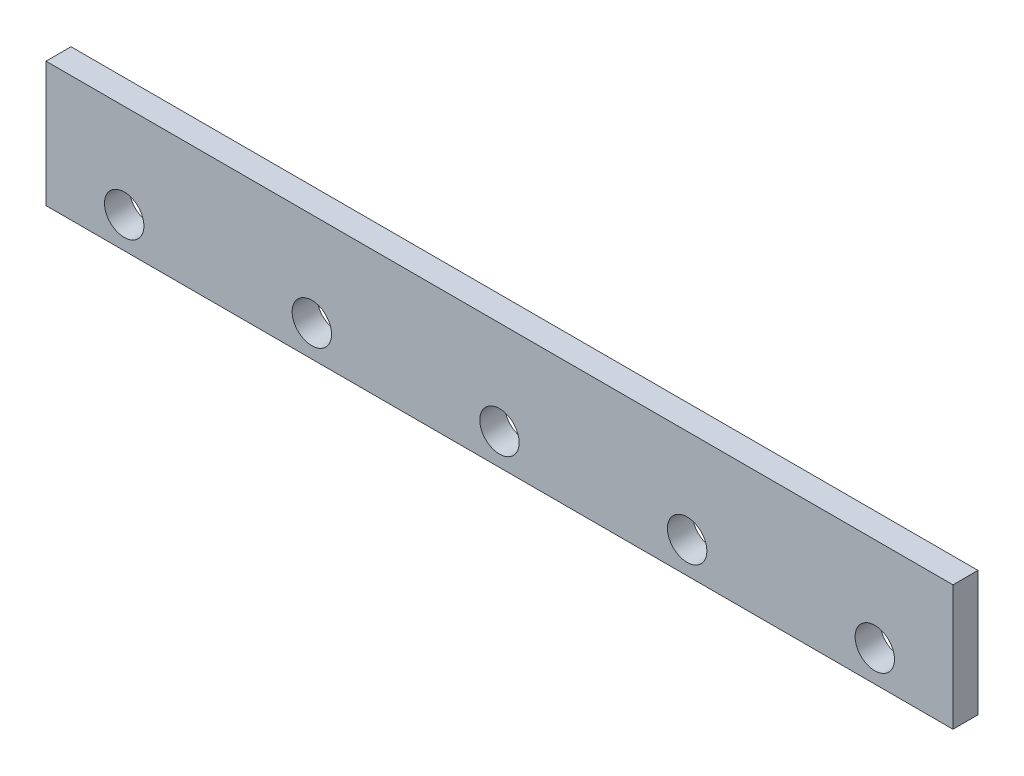
SolidWorks part; units mm, degrees
ref_plane "Front Plane" through (0, 0, 0) normal (0, 0, 1) x (1, 0, 0)
ref_plane "Top Plane" through (0, 0, 0) normal (0, 1, 0) x (1, 0, 0)
ref_plane "Right Plane" through (0, 0, 0) normal (1, 0, 0) x (0, 0, -1)
sketch "Sketch1" plane through (0, 0, 0) normal (0, 0, 1) x (1, 0, 0)
  line L1 (0, 0) -> (580, 0)
  line L2 (0, 0) -> (0, 80)
  line L3 (0, 80) -> (580, 80)
  line L4 (580, 0) -> (580, 80)
  circle A0 centre (50, 20) radius 12.6
  circle A1 centre (170, 20) radius 12.6
  circle A2 centre (290, 20) radius 12.6
  circle A3 centre (410, 20) radius 12.6
  circle A4 centre (530, 20) radius 12.6
  dimension "D3" = 25.2
  dimension "D10" = 25.2
  dimension "D11" = 25.2
  dimension "D12" = 25.2
  dimension "D13" = 25.2
  dimension "D1" = 580
  dimension "D2" = 80
  dimension "D4" = 50
  dimension "D5" = 20
  dimension "D6" = 120
  dimension "D7" = 120
  dimension "D8" = 120
  dimension "D9" = 120
  dimension "D14" = 50
extrude "Boss-Extrude1" add sketch "Sketch1" along normal blind 16
